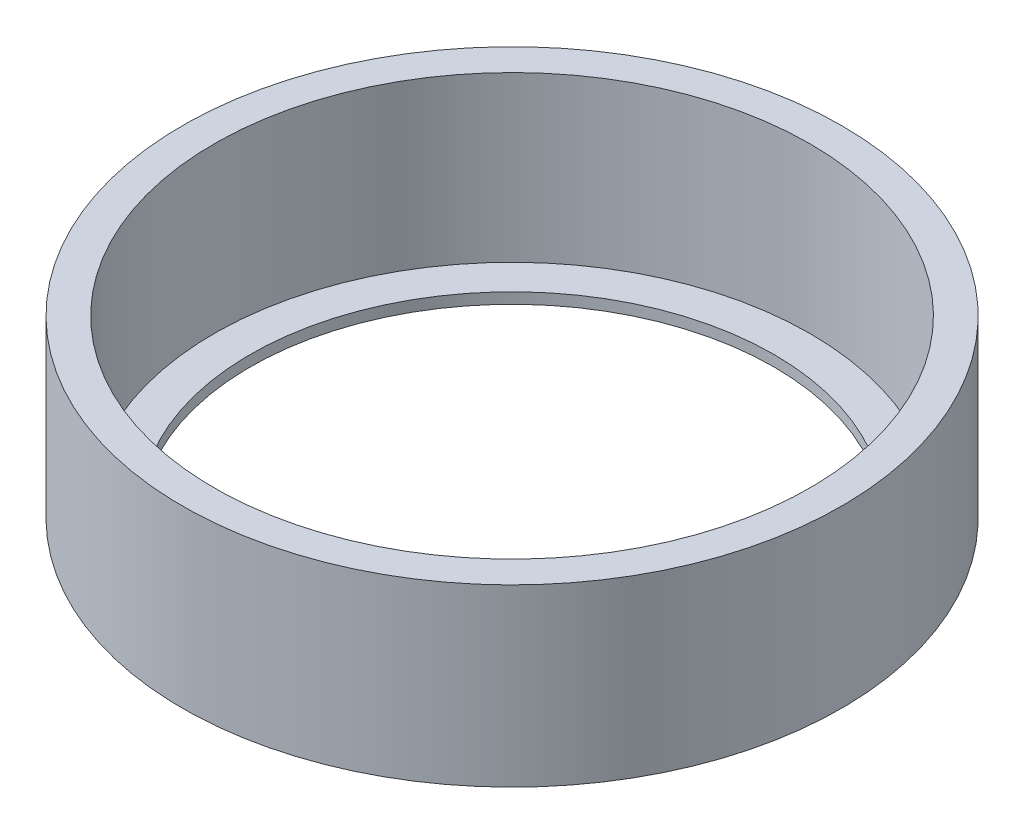
SolidWorks part; units mm, degrees
ref_plane "Front Plane" through (0, 0, 0) normal (0, 0, 1) x (1, 0, 0)
ref_plane "Top Plane" through (0, 0, 0) normal (0, 1, 0) x (1, 0, 0)
ref_plane "Right Plane" through (0, 0, 0) normal (1, 0, 0) x (0, 0, -1)
sketch "Sketch1" plane through (0, 0, 0) normal (0, 0, 1) x (1, 0, 0)
  line L0 (0, 0) -> (0, 33.782) construction
  line L1 (46.355, 0) -> (46.355, 24.638)
  line L2 (41.91, 1.524) -> (41.91, 24.638)
  line L3 (41.91, 1.524) -> (36.83, 1.524)
  line L4 (36.83, 1.524) -> (36.83, 0)
  line L5 (36.83, 0) -> (46.355, 0)
  line L6 (46.355, 24.638) -> (41.91, 24.638)
  point P8 (0, 0)
  dimension "D1" = 24.638
  dimension "D2" = 92.71
  dimension "D3" = 83.82
  dimension "D4" = 73.66
  dimension "D5" = 1.524
revolve "Revolve1" add sketch "Sketch1" angle 360 about L0
